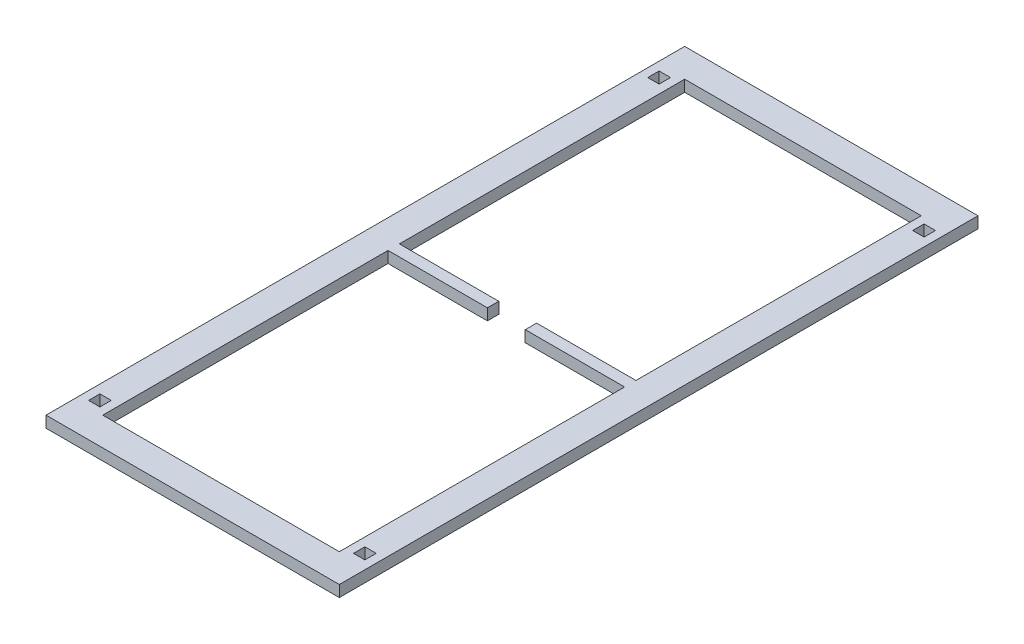
SolidWorks part; units mm, degrees
ref_plane "Front Plane" through (0, 0, 0) normal (0, 0, 1) x (1, 0, 0)
ref_plane "Top Plane" through (0, 0, 0) normal (0, 1, 0) x (1, 0, 0)
ref_plane "Right Plane" through (0, 0, 0) normal (1, 0, 0) x (0, 0, -1)
sketch "Sketch1" plane through (0, 0, 0) normal (0, 1, 0) x (1, 0, 0)
  line L0 (150, -332.5) -> (150, 332.5)
  line L1 (130, -312.5) -> (-130, -312.5)
  line L2 (130, -312.5) -> (130, 312.5)
  line L3 (130, 312.5) -> (-130, 312.5)
  line L4 (-130, -312.5) -> (-130, 312.5)
  line L5 (130, -312.5) -> (-130, 312.5) construction
  line L6 (130, 312.5) -> (-130, -312.5) construction
  line L7 (150, 332.5) -> (-150, 332.5)
  line L8 (-150, -332.5) -> (-150, 332.5)
  line L9 (150, -332.5) -> (-150, -332.5)
  line L10 (-125, -307.5) -> (-125, 307.5)
  line L11 (125, 307.5) -> (-125, 307.5)
  line L12 (125, -307.5) -> (125, 307.5)
  line L13 (125, -307.5) -> (-125, -307.5)
  line L14 (155, -337.5) -> (155, 337.5)
  line L15 (155, 337.5) -> (-155, 337.5)
  line L16 (-155, -337.5) -> (-155, 337.5)
  line L17 (155, -337.5) -> (-155, -337.5)
  point P0 (0, 0)
  dimension "D1" = 625
  dimension "D2" = 260
  dimension "D3" = 20
  dimension "D4" = 5
  dimension "D5" = 5
extrude "Boss-Extrude1" add sketch "Sketch1" along normal blind 12 contours L17 L14 L15 L16 L0 L9 L8 L7 | L9 L0 L7 L8 L1 L4 L3 L2 | L4 L1 L2 L3 L12 L13 L10 L11
sketch "Sketch2" plane through (0, 12, 0) normal (0, 1, 0) x (1, 0, 0)
  line L1 (-134, -301.5) -> (-146, -301.5)
  line L2 (-134, -301.5) -> (-134, -289.5)
  line L3 (-134, -289.5) -> (-146, -289.5)
  line L4 (-146, -301.5) -> (-146, -289.5)
  line L5 (-134, -301.5) -> (-146, -289.5) construction
  line L6 (-134, -289.5) -> (-146, -301.5) construction
  line L9 (-146, 301.5) -> (-134, 301.5)
  line L10 (-146, 301.5) -> (-146, 289.5)
  line L11 (-146, 289.5) -> (-134, 289.5)
  line L12 (-134, 301.5) -> (-134, 289.5)
  line L13 (134, 301.5) -> (146, 301.5)
  line L14 (134, 301.5) -> (134, 289.5)
  line L15 (134, 289.5) -> (146, 289.5)
  line L16 (146, 301.5) -> (146, 289.5)
  line L17 (134, -289.5) -> (146, -289.5)
  line L18 (134, -289.5) -> (134, -301.5)
  line L19 (134, -301.5) -> (146, -301.5)
  line L20 (146, -289.5) -> (146, -301.5)
  line L40 (-150, -332.5) -> (-150, 332.5) construction
  line L41 (150, -332.5) -> (-150, -332.5) construction
  line L42 (150, -332.5) -> (150, 332.5) construction
  line L43 (150, 332.5) -> (-150, 332.5) construction
  point P0 (-140, -295.5)
  dimension "D1" = 12
  dimension "D2" = 12
  dimension "D3" = 31
  dimension "D4" = 4
  dimension "D5" = 4
  dimension "D6" = 12
  dimension "D7" = 12
  dimension "D8" = 4
  dimension "D9" = 31
extrude "Cut-Extrude1" cut sketch "Sketch2" against normal through all both and the other way through all from surface at 0 starting at face at (0, 12, 0)
sketch "Sketch3" plane through (0, 12, 0) normal (0, 1, 0) x (1, 0, 0)
  line L1 (-125, 6) -> (125, 6)
  line L2 (-125, 6) -> (-125, -6)
  line L3 (-125, -6) -> (125, -6)
  line L4 (125, 6) -> (125, -6)
  line L6 (125, -307.5) -> (125, 307.5) construction
  line L7 (-20, -6) -> (20, -6)
  line L8 (-20, -6) -> (-20, 6)
  line L9 (-20, 6) -> (20, 6)
  line L10 (20, -6) -> (20, 6)
  line L11 (-125, -307.5) -> (-125, 307.5) construction
  point P4 (-125, 6)
  point P6 (125, -6)
  point P8 (-125, 0)
  point P15 (0, 0)
  dimension "D1" = 12
  dimension "D2" = 40
  dimension "D3" = 20
extrude "Boss-Extrude2" add sketch "Sketch3" against normal blind 12
